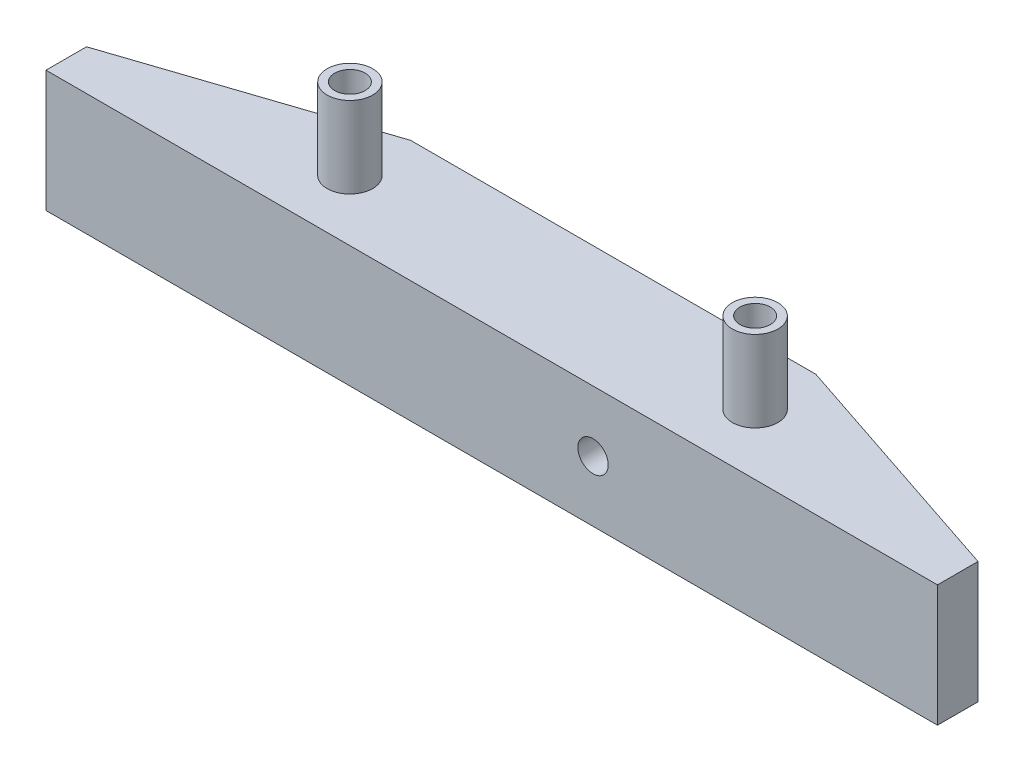
SolidWorks part; units mm, degrees
ref_plane "Front Plane" through (0, 0, 0) normal (0, 0, 1) x (1, 0, 0)
ref_plane "Top Plane" through (0, 0, 0) normal (0, 1, 0) x (1, 0, 0)
ref_plane "Right Plane" through (0, 0, 0) normal (1, 0, 0) x (0, 0, -1)
sketch "Sketch1" plane through (0, 0, 0) normal (0, 1, 0) x (1, 0, 0)
  line L0 (0, 0) -> (88, 0)
  line L1 (88, 0) -> (88, 4)
  line L2 (88, 4) -> (64, 12)
  line L3 (64, 12) -> (24, 12)
  line L4 (24, 12) -> (0, 4)
  line L5 (0, 4) -> (0, 0)
  point P3 (44, 12)
  point P8 (44, 0)
  dimension "D1" = 88
  dimension "D2" = 4
  dimension "D3" = 12
  dimension "D4" = 40
extrude "Boss-Extrude1" add sketch "Sketch1" along normal blind 12
sketch "Sketch2" plane through (0, 0, 0) normal (0, -1, 0) x (-1, 0, 0)
  line L0 (-44, 12) -> (-44, 0) construction
  line L1 (-64, 12) -> (-24, 12) construction
  line L2 (0, 0) -> (-88, 0) construction
  circle A0 centre (-24, 6) radius 2.5
  circle A1 centre (-64, 6) radius 2.5
  point P4 (0, 0)
  point P13 (-44, 6)
  dimension "D1" = 5
extrude "Cut-Extrude1" cut sketch "Sketch2" against normal blind 5
sketch "Sketch3" plane through (0, 5, 0) normal (0, -1, 0) x (-1, 0, 0)
  circle A0 centre (-24, 6) radius 1.5
  circle A1 centre (-64, 6) radius 1.5
  dimension "D1" = 3
extrude "Cut-Extrude2" cut sketch "Sketch3" against normal through all
sketch "Sketch4" plane through (0, 12, 0) normal (0, 1, 0) x (1, 0, 0)
  circle A0 centre (24, 6) radius 1.5
  circle A1 centre (24, 6) radius 2.25
  circle A2 centre (64, 6) radius 2.2946
  circle A3 centre (64, 6) radius 2.25
  circle A4 centre (64, 6) radius 1.5 construction
  circle A5 centre (64, 6) radius 1.5
  circle M3 centre (24, 6) radius 1.5
  circle M4 centre (64, 6) radius 1.5
  dimension "D2" = 4.5
extrude "Boss-Extrude2" add sketch "Sketch4" along normal blind 8 contours A1 M3 | A3 M4
sketch "Sketch5" plane through (0, 0, -12) normal (0, 0, -1) x (-1, 0, 0)
  line L1 (-64, 12) -> (-64, 0) construction
  circle A0 centre (-54, 6) radius 5
  dimension "D1" = 10
  dimension "D2" = 10
extrude "Cut-Extrude3" cut sketch "Sketch5" against normal blind 3
sketch "Sketch6" plane through (0, 0, -9) normal (0, 0, -1) x (-1, 0, 0)
  circle A0 centre (-54, 6) radius 1.5
  dimension "D1" = 3
extrude "Cut-Extrude4" cut sketch "Sketch6" against normal through all
